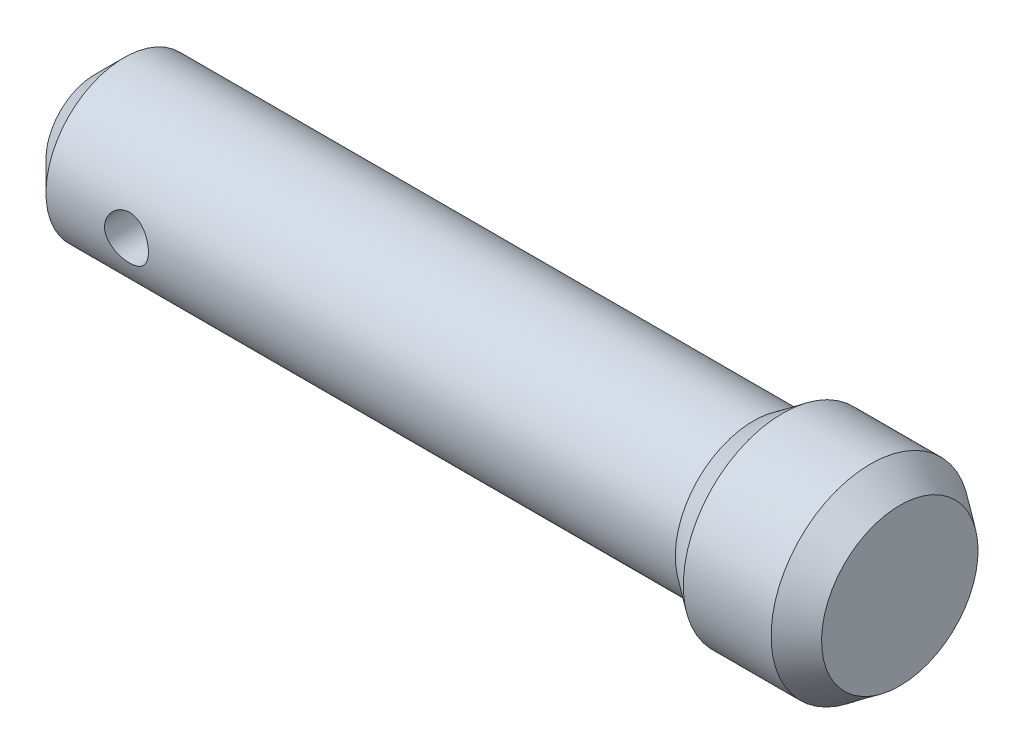
SolidWorks part; units mm, degrees
ref_plane "Alzado" through (0, 0, 0) normal (0, 0, 1) x (1, 0, 0)
ref_plane "Planta" through (0, 0, 0) normal (0, 1, 0) x (1, 0, 0)
ref_plane "Vista lateral" through (0, 0, 0) normal (1, 0, 0) x (0, 0, -1)
sketch "Croquis1" plane through (0, 0, 0) normal (0, 0, 1) x (1, 0, 0)
  line L0 (0, 0) -> (86, 0)
  line L1 (0, 0) -> (0, -10.6915)
  line L2 (-4, -10.6915) -> (106, -10.6915)
  line L3 (-4, -4) -> (-4, -10.6915)
  line L4 (0, 0) -> (-4, -4)
  line L6 (102, 2.8998) -> (102, -10.6915)
  line L7 (86, -10.6915) -> (86, 0)
  line L8 (90, 2.8998) -> (90, -10.6915)
  line L9 (90, 2.8998) -> (102, 2.8998)
  line L10 (86, 0) -> (90, 2.8998)
  line L11 (102, 2.8998) -> (106, 0)
  line L12 (106, 0) -> (106, -10.6915)
  dimension "D2" = 45
  dimension "D3" = 20
  dimension "D4" = 4
  dimension "D5" = 12
  dimension "D6" = 4
  dimension "D8" = 110
revolve "Revolución3" add sketch "Croquis1" angle 360 about L2
sketch "Croquis2" plane through (0, 0, 0) normal (0, 0, 1) x (1, 0, 0)
  line L0 (-4, -10.6915) -> (90, -10.6915) construction
  line L1 (-4, -4) -> (-4, -17.3831) construction
  line L2 (90, -24.2829) -> (90, 2.8998) construction
  circle A0 centre (11, -10.6915) radius 3
  dimension "D1" = 15
extrude "Cortar-Extruir1" cut sketch "Croquis2" against normal through all both and the other way through all
